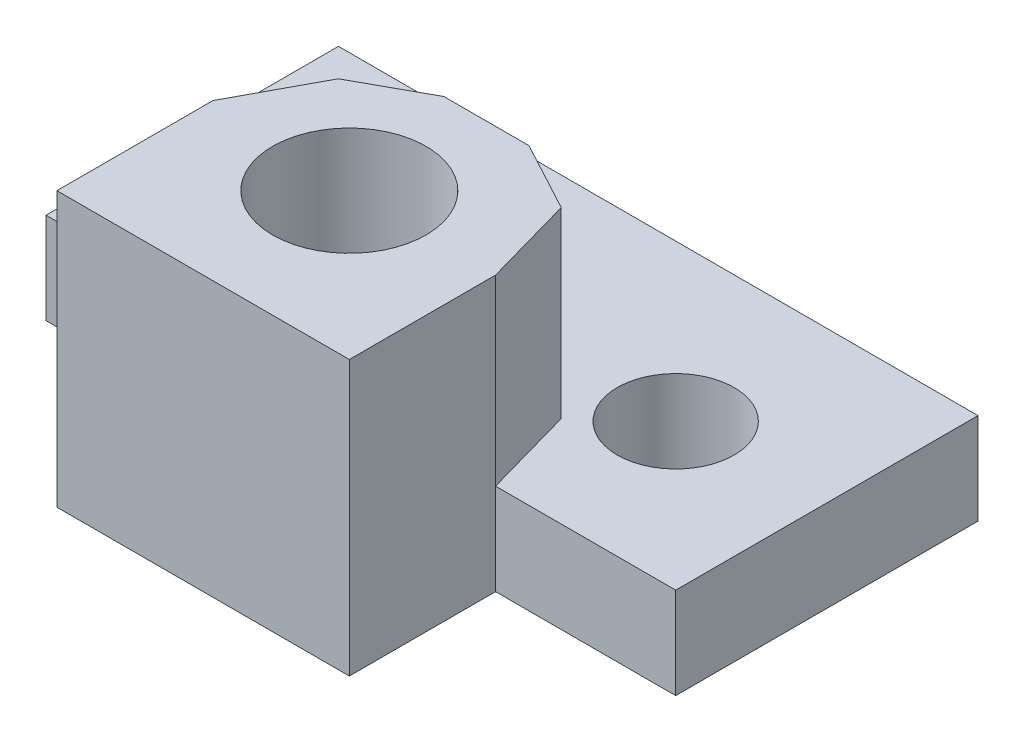
SolidWorks part; units mm, degrees
ref_plane "Front Plane" through (0, 0, 0) normal (0, 0, 1) x (1, 0, 0)
ref_plane "Top Plane" through (0, 0, 0) normal (0, 1, 0) x (1, 0, 0)
ref_plane "Right Plane" through (0, 0, 0) normal (1, 0, 0) x (0, 0, -1)
sketch "Sketch1" plane through (0, 0, 0) normal (0, 1, 0) x (1, 0, 0)
  line L0 (-8.5681, 2.3249) -> (-8.5681, -5.6751)
  line L1 (-8.5681, -5.6751) -> (-4, -5.6751)
  line L2 (-4, -5.6751) -> (-4, -9.9448)
  line L3 (-4, -9.9448) -> (4, -9.9448)
  line L4 (4, -9.9448) -> (4, -5.9448)
  line L5 (4, -5.9448) -> (8.9281, -5.9448)
  line L6 (8.9281, -5.9448) -> (8.9281, 2.3249)
  line L7 (8.9281, 2.3249) -> (-8.5681, 2.3249)
  circle A0 centre (-4.5681, -1.6751) radius 1.6
  circle A1 centre (4.9281, -1.9448) radius 1.6
  circle A2 centre (0, -5.9448) radius 2.5
  point P14 (0, 0)
  dimension "D2" = 3.2
  dimension "D7" = 5
  dimension "D1" = 9.5
  dimension "D3" = 4
  dimension "D4" = 4
  dimension "D5" = 4
  dimension "D6" = 4
  dimension "D8" = 4
  dimension "D9" = 4
  dimension "D10" = 4
  dimension "D11" = 4
extrude "Boss-Extrude1" add sketch "Sketch1" along normal blind 2.5
sketch "Sketch3" plane through (0, 2.5, 0) normal (0, 1, 0) x (1, 0, 0)
  line L0 (4, -9.9448) -> (-4, -9.9448)
  line L1 (-4, -9.9448) -> (-4, -5.6751)
  line L2 (-4, -5.6751) -> (-2.8019, -3.4465)
  line L3 (-2.8019, -3.4465) -> (-0.9382, -2.4215)
  line L4 (-0.9382, -2.4215) -> (1.3914, -2.4215)
  line L5 (1.3914, -2.4215) -> (3.298, -3.4465)
  line L6 (3.298, -3.4465) -> (4, -5.9448)
  line L7 (4, -5.9448) -> (4, -9.9448)
  circle A0 centre (0, -5.9448) radius 2.5 construction
  circle A1 centre (0, -5.9448) radius 2.1
  point P12 (0, -3.4448)
  point P13 (2.5, -5.9448)
extrude "Boss-Extrude2" add sketch "Sketch3" along normal blind 5
equation "\"padding\"=4"
equation "\"D3@Sketch1\"=\"padding\""
equation "\"D4@Sketch1\"=\"padding\""
equation "\"D5@Sketch1\"=\"padding\""
equation "\"D6@Sketch1\"=\"padding\""
equation "\"D9@Sketch1\"=\"padding\""
equation "\"D10@Sketch1\"=\"padding\""
equation "\"D11@Sketch1\"=\"padding\""
